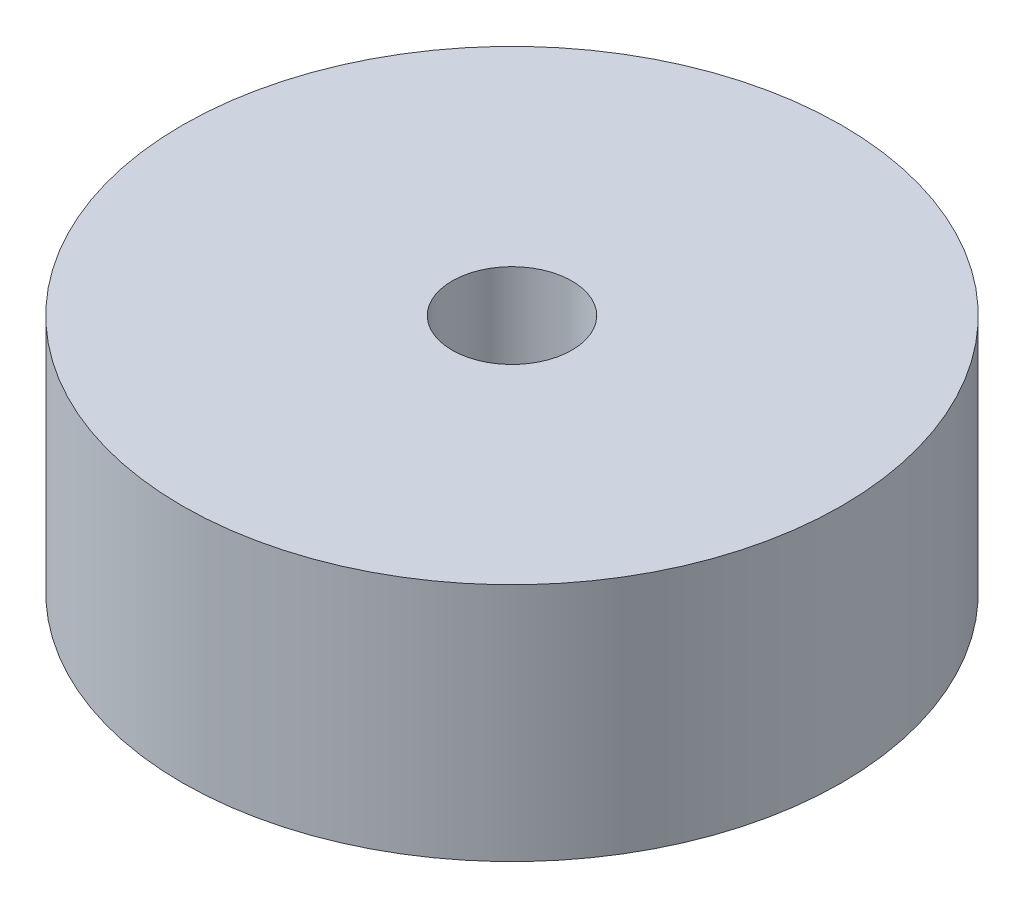
SolidWorks part; units mm, degrees
ref_plane "Front Plane" through (0, 0, 0) normal (0, 0, 1) x (1, 0, 0)
ref_plane "Top Plane" through (0, 0, 0) normal (0, 1, 0) x (1, 0, 0)
ref_plane "Right Plane" through (0, 0, 0) normal (1, 0, 0) x (0, 0, -1)
sketch "Sketch1" plane through (0, 0, 0) normal (0, 1, 0) x (1, 0, 0)
  circle A0 centre (0, 0) radius 34.925
  circle A1 centre (0, 0) radius 6.35
  dimension "D1" = 69.85
  dimension "D2" = 12.7
extrude "Boss-Extrude1" add sketch "Sketch1" along normal blind 25.4 contours A0
